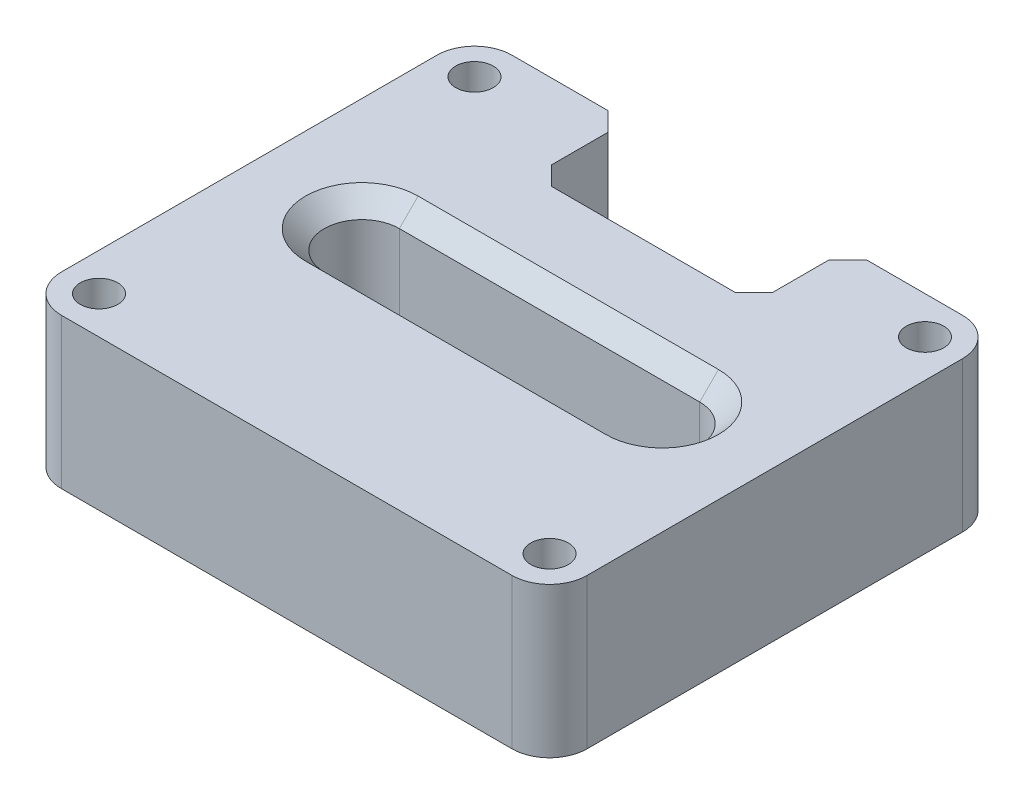
SolidWorks part; units mm, degrees
ref_plane "Front Plane" through (0, 0, 0) normal (0, 0, 1) x (1, 0, 0)
ref_plane "Top Plane" through (0, 0, 0) normal (0, 1, 0) x (1, 0, 0)
ref_plane "Right Plane" through (0, 0, 0) normal (1, 0, 0) x (0, 0, -1)
sketch "Sketch1" plane through (0, 0, 0) normal (0, 1, 0) x (1, 0, 0)
  line L0 (-40, 0) -> (40, 0) construction
  line L1 (-60, 60) -> (-34.4352, 60)
  line L2 (-70, 50) -> (-70, -50)
  line L3 (-60, -60) -> (60, -60)
  line L4 (70, 50) -> (70, -50)
  line L5 (-70, 60) -> (70, -60) construction
  line L6 (-70, -60) -> (70, 60) construction
  line L7 (-40, 10) -> (40, 10)
  line L8 (-40, -10) -> (40, -10)
  line L9 (34.4352, 60) -> (60, 60)
  line L11 (-29.4352, 55) -> (-29.4352, 40)
  line L12 (-24.4352, 35) -> (24.4352, 35)
  line L13 (29.4352, 55) -> (29.4352, 40)
  line L14 (-29.4352, 40) -> (-24.4352, 35)
  line L15 (24.4352, 35) -> (29.4352, 40)
  line L16 (34.4352, 60) -> (29.4352, 55)
  line L17 (-34.4352, 60) -> (-29.4352, 55)
  arc A0 (-40, 10) -> (-40, -10) centre (-40, 0) ccw
  arc A1 (40, -10) -> (40, 10) centre (40, 0) ccw
  arc A2 (-70, -50) -> (-60, -60) centre (-60, -50) ccw
  arc A3 (60, -60) -> (70, -50) centre (60, -50) ccw
  arc A4 (60, 60) -> (70, 50) centre (60, 50) cw
  arc A5 (-60, 60) -> (-70, 50) centre (-60, 50) ccw
  circle A6 centre (-60, 50) radius 5
  circle A7 centre (60, 50) radius 5
  circle A8 centre (60, -50) radius 5
  circle A9 centre (-60, -50) radius 5
  point P0 (0, 0)
  point P8 (0, 0)
  point P29 (0, 60)
  point P30 (29.4352, 35)
  point P32 (-29.4352, 35)
  point P34 (29.4352, 60)
  point P36 (-29.4352, 60)
  dimension "D4" = 10
  dimension "D5" = 10
  dimension "D6" = 10
  dimension "D1" = 140
  dimension "D2" = 120
  dimension "D3" = 80
  dimension "D7" = 25
  dimension "D8" = 58.8705
extrude "Boss-Extrude2" add sketch "Sketch1" along normal blind 40
chamfer "Chamfer1" distance 5 angle 45 8 edges at (50, 40, 0) (0, 40, -10) (0, 40, 10) (-50, 40, 0) (50, 0, 0) (0, 0, -10) (0, 0, 10) (-50, 0, 0)
